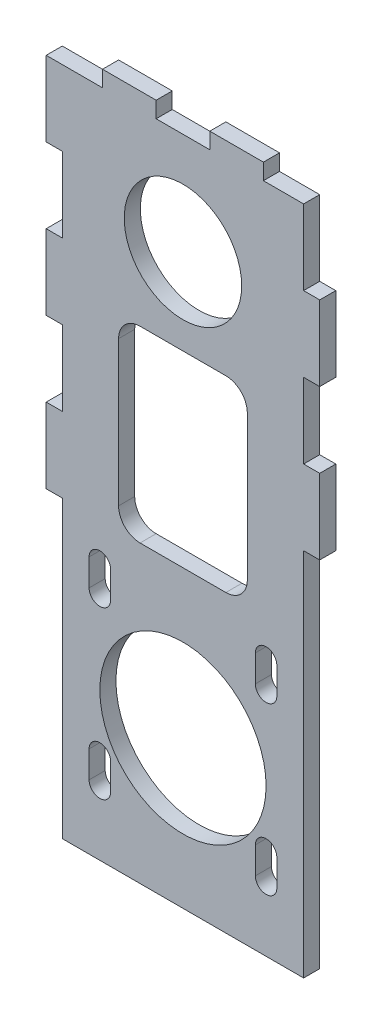
SolidWorks part; units mm, degrees
material "PC High Viscosity"
ref_plane "Front Plane" through (0, 0, 0) normal (0, 0, 1) x (1, 0, 0)
ref_plane "Top Plane" through (0, 0, 0) normal (0, 1, 0) x (1, 0, 0)
ref_plane "Right Plane" through (0, 0, 0) normal (1, 0, 0) x (0, 0, -1)
sketch "Sketch1" plane through (0, 0, 0) normal (0, 0, 1) x (1, 0, 0)
  line L1 (-22.5, -35) -> (22.5, -35)
  line L2 (-22.5, -35) -> (-22.5, 35)
  line L3 (-22.5, 35) -> (22.5, 35)
  line L4 (22.5, -35) -> (22.5, 35)
  line L5 (-22.5, -35) -> (22.5, 35) construction
  line L6 (-22.5, 35) -> (22.5, -35) construction
  point P0 (0, 0)
  dimension "D1" = 70
  dimension "D2" = 45
extrude "Boss-Extrude1" add sketch "Sketch1" along normal blind 3 contours L2 L3 L4 L1
sketch "Sketch2" plane through (0, 0, 3) normal (0, 0, 1) x (1, 0, 0)
  line L0 (-22.5, -35) -> (22.5, -35) construction
  line L1 (-12, 0) -> (12, 0)
  line L2 (-12, 0) -> (-12, -35)
  line L3 (-12, -35) -> (12, -35)
  line L4 (12, 0) -> (12, -35)
  line L5 (-12, 0) -> (12, -35) construction
  line L6 (-12, -35) -> (12, 0) construction
  circle A0 centre (0, 16) radius 10.95
  point P2 (0, -17.5)
  dimension "D1" = 21.9
  dimension "D2" = 16
  dimension "D3" = 24
  dimension "D4" = 35
extrude "Cut-Extrude1" cut sketch "Sketch2" against normal through all
sketch "Sketch4" plane through (0, 0, 3) normal (0, 0, 1) x (1, 0, 0)
  line L0 (0, 35) -> (0, 41.52) construction
  line L1 (-15, 35) -> (-5, 35)
  line L2 (-15, 35) -> (-15, 38)
  line L3 (-15, 38) -> (-5, 38)
  line L4 (-5, 35) -> (-5, 38)
  line L5 (-22.5, 35) -> (22.5, 35) construction
  line L6 (5, 35) -> (5, 38)
  line L7 (15, 38) -> (5, 38)
  line L8 (15, 35) -> (15, 38)
  line L9 (15, 35) -> (5, 35)
  dimension "D1" = 3
  dimension "D2" = 10
  dimension "D3" = 10
extrude "Boss-Extrude3" add sketch "Sketch4" against normal up to surface (3 mm away) up to face at (0, -8.75, 0)
sketch "Sketch3" plane through (0, 0, 0) normal (0, 0, -1) x (-1, 0, 0)
  line L0 (22.5, 7) -> (22.5, -7)
  line L1 (22.5, 35) -> (25.5, 35)
  line L2 (22.5, 35) -> (22.5, 21)
  line L3 (22.5, 21) -> (25.5, 21)
  line L4 (25.5, 35) -> (25.5, 21)
  line L5 (22.5, 7) -> (25.5, 7)
  line L6 (25.5, 7) -> (25.5, -7)
  line L7 (22.5, -7) -> (25.5, -7)
  line L8 (22.5, -21) -> (22.5, -35)
  line L9 (22.5, -21) -> (25.5, -21)
  line L10 (25.5, -21) -> (25.5, -35)
  line L11 (22.5, -35) -> (25.5, -35)
  line L12 (22.5, -35) -> (22.5, 35) construction
  line L13 (-22.5, -35) -> (-22.5, 35) construction
  line L14 (-22.5, 21) -> (-25.5, 21)
  line L15 (-22.5, 21) -> (-22.5, 7)
  line L16 (-22.5, 7) -> (-25.5, 7)
  line L17 (-25.5, 21) -> (-25.5, 7)
  line L18 (22.5, -35) -> (12, -35) construction
  line L19 (-22.5, -7) -> (-25.5, -7)
  line L20 (-22.5, -7) -> (-22.5, -21)
  line L21 (-22.5, -21) -> (-25.5, -21)
  line L22 (-25.5, -7) -> (-25.5, -21)
  dimension "D1" = 3
  dimension "D2" = 14
  dimension "D3" = 3
extrude "Boss-Extrude2" add sketch "Sketch3" against normal up to surface (3 mm away) up to face at (-0.7813, 13.875, 3)
sketch "Sketch5" plane through (0, 0, 3) normal (0, 0, 1) x (1, 0, 0)
  line L0 (-22.5, -21) -> (-22.5, -7) construction
  line L1 (22.5, -35) -> (-22.5, -35)
  line L2 (22.5, -35) -> (22.5, -90)
  line L3 (22.5, -90) -> (-22.5, -90)
  line L4 (-22.5, -35) -> (-22.5, -90)
  dimension "D1" = 55
extrude "Boss-Extrude4" add sketch "Sketch5" against normal up to surface (3 mm away) up to face at (-0.5781, 5.8437, 0)
fillet "Fillet1" radius 4 4 edges at (12, 0, 1.5) (-12, 0, 1.5) (12, -35, 1.5) (-12, -35, 1.5)
sketch "Sketch6" plane through (0, 0, 0) normal (0, 0, -1) x (-1, 0, 0)
  line L0 (0, -35) -> (0, -90) construction
  line L1 (15.5, -47) -> (-15.5, -47) construction
  line L2 (15.5, -47) -> (15.5, -78) construction
  line L3 (15.5, -78) -> (-15.5, -78) construction
  line L4 (-15.5, -47) -> (-15.5, -78) construction
  line L5 (15.5, -47) -> (-15.5, -78) construction
  line L6 (15.5, -78) -> (-15.5, -47) construction
  line L7 (8, -35) -> (-8, -35) construction
  line L8 (-22.5, -90) -> (22.5, -90) construction
  line L9 (15.5, -78) -> (15.5, -73) construction
  line L10 (13.5, -78) -> (13.5, -73)
  line L11 (17.5, -78) -> (17.5, -73)
  line L12 (-15.5, -78) -> (-15.5, -73) construction
  line L13 (-17.5, -78) -> (-17.5, -73)
  line L14 (-13.5, -78) -> (-13.5, -73)
  line L15 (-15.5, -47) -> (-15.5, -42) construction
  line L16 (-17.5, -47) -> (-17.5, -42)
  line L17 (-13.5, -47) -> (-13.5, -42)
  line L18 (15.5, -47) -> (15.5, -42) construction
  line L19 (13.5, -47) -> (13.5, -42)
  line L20 (17.5, -47) -> (17.5, -42)
  arc A0 (13.5, -78) -> (17.5, -78) centre (15.5, -78) ccw
  arc A1 (17.5, -73) -> (13.5, -73) centre (15.5, -73) ccw
  arc A2 (-17.5, -78) -> (-13.5, -78) centre (-15.5, -78) ccw
  arc A3 (-13.5, -73) -> (-17.5, -73) centre (-15.5, -73) ccw
  arc A4 (-17.5, -47) -> (-13.5, -47) centre (-15.5, -47) ccw
  arc A5 (-13.5, -42) -> (-17.5, -42) centre (-15.5, -42) ccw
  arc A6 (13.5, -47) -> (17.5, -47) centre (15.5, -47) ccw
  arc A7 (17.5, -42) -> (13.5, -42) centre (15.5, -42) ccw
  circle A8 centre (0, -62.5) radius 15.5
  point P0 (0, -62.5)
  point P14 (15.5, -75.5)
  point P19 (-15.5, -75.5)
  point P25 (-15.5, -44.5)
  point P31 (15.5, -44.5)
  dimension "D2" = 2
  dimension "D1" = 31
  dimension "D3" = 5
extrude "Cut-Extrude2" cut sketch "Sketch6" against normal blind 10
equation "\"pulley_pitch_diam\"= 12.73mm"
equation "\"pulley_total_width\"= 16mm"
equation "\"belt_width\"= 6mm"
equation "\"material_thickness\"= 3mm"
equation "\"D1@Boss-Extrude1\"=\"material_thickness\""
equation "\"shaft_diam\"= 8mm"
equation "\"D1@Sketch2\"=\"bearing_od\" - 0.1mm"
equation "\"pulley_total_diam\"= 16mm"
equation "\"D2@Sketch2\"=\"pulley_total_diam\" "
equation "\"D3@Sketch2\"=\"pulley_total_width\" * 1.5"
equation "\"D1@Sketch3\"=\"material_thickness\""
equation "\"bearing_od\"= 22mm"
equation "\"bearing_thickness\"= 7mm"
equation "\"D1@Sketch4\"=\"material_thickness\""
